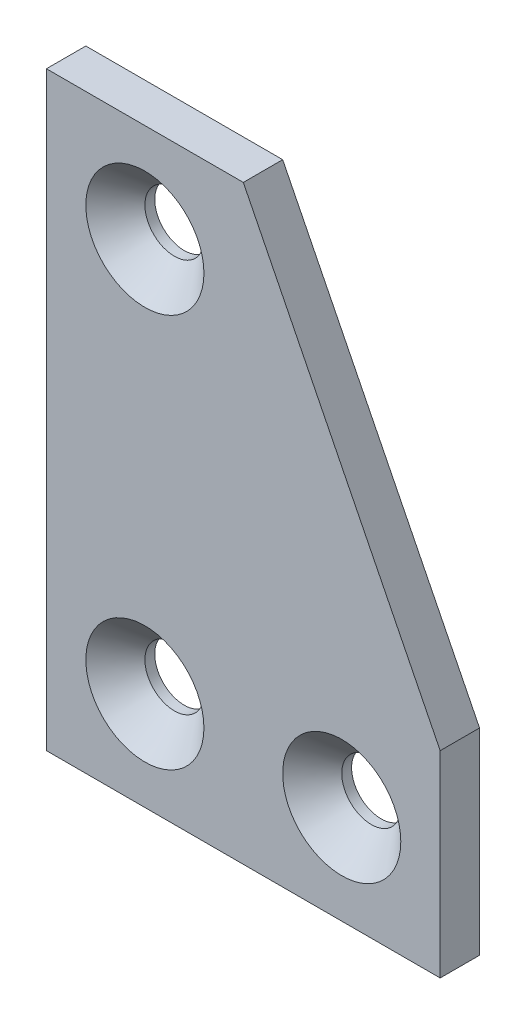
SolidWorks part; units mm, degrees
ref_plane "Front Plane" through (0, 0, 0) normal (0, 0, 1) x (1, 0, 0)
ref_plane "Top Plane" through (0, 0, 0) normal (0, 1, 0) x (1, 0, 0)
ref_plane "Right Plane" through (0, 0, 0) normal (1, 0, 0) x (0, 0, -1)
sketch "Sketch1" plane through (0, 0, 0) normal (0, 0, 1) x (1, 0, 0)
  line L2 (-20, -30) -> (-20, 30)
  line L3 (-20, 30) -> (0, 30)
  line L5 (-20, -30) -> (0, 30) construction
  line L6 (-20, -30) -> (20, -30)
  line L7 (20, -30) -> (20, -10)
  line L8 (0, 30) -> (20, -10)
  line L9 (0, 30) -> (0, -30) construction
  point P0 (0, 0)
  point P4 (0, 0)
  point P9 (0, 0)
  point P10 (0, 0)
  dimension "D1" = 60
  dimension "D2" = 20
  dimension "D3" = 40
  dimension "D4" = 20
extrude "Boss-Extrude1" add sketch "Sketch1" along normal mid plane 4
sketch "Sketch2" plane through (0, 0, 2) normal (0, 0, 1) x (1, 0, 0)
  line L0 (-10, 20) -> (-10, -20) construction
  line L1 (-10, -20) -> (10, -20) construction
  line L2 (10, -20) -> (10, 20) construction
  line L3 (10, 20) -> (-10, 20) construction
  line L4 (-10, 20) -> (10, -20) construction
  circle A0 centre (-10, 20) radius 3
  circle A1 centre (10, 20) radius 3
  circle A2 centre (-10, -20) radius 3
  circle A3 centre (10, -20) radius 3
  point P8 (0, 0)
  dimension "D1" = 6
  dimension "D2" = 40
  dimension "D3" = 20
extrude "Cut-Extrude1" cut sketch "Sketch2" against normal through all contours A0 | A2 | A3
chamfer "Chamfer1" distance 3 angle 45 3 edges at (13, -20, 2) (-7, -20, 2) (-7, 20, 2)
fillet "Fillet1" [suppressed] radius 1
